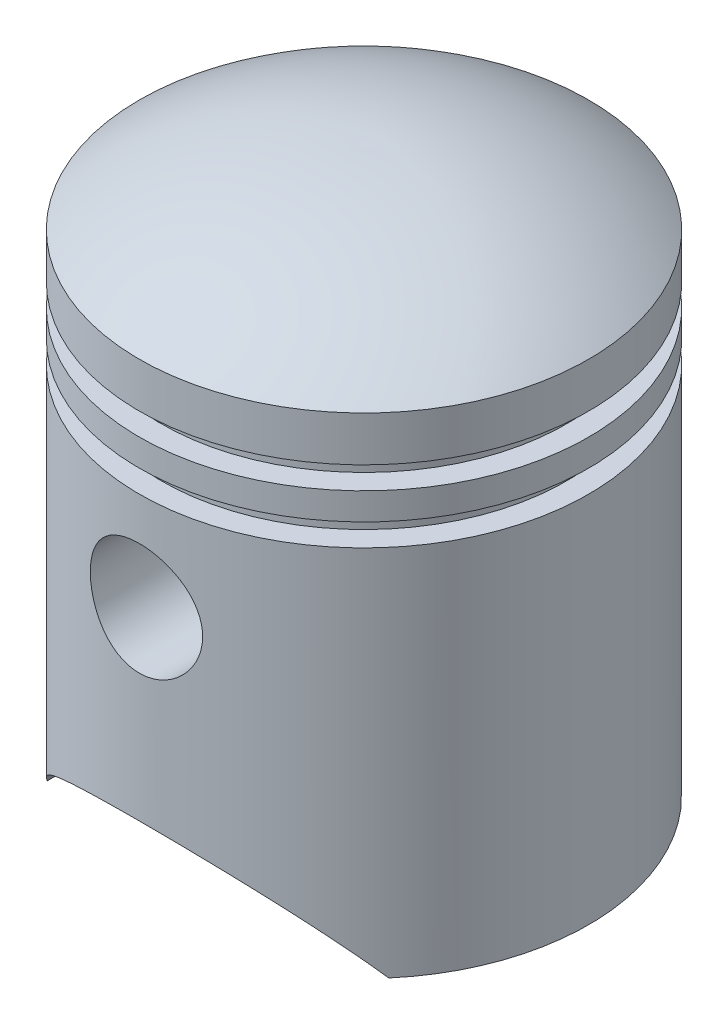
SolidWorks part; units mm, degrees
ref_plane "Front Plane" through (0, 0, 0) normal (0, 0, 1) x (1, 0, 0)
ref_plane "Top Plane" through (0, 0, 0) normal (0, 1, 0) x (1, 0, 0)
ref_plane "Right Plane" through (0, 0, 0) normal (1, 0, 0) x (0, 0, -1)
sketch "Sketch1" plane through (0, 0, 0) normal (0, 0, 1) x (1, 0, 0)
  line L0 (0, 1587.5) -> (0, 1536.6838)
  line L1 (584.2, 0) -> (635, 0)
  line L2 (635, 0) -> (635, 1054.1)
  line L3 (635, 1054.1) -> (571.5, 1054.1)
  line L4 (571.5, 1054.1) -> (571.5, 1117.6)
  line L5 (571.5, 1117.6) -> (635, 1117.6)
  line L6 (635, 1117.6) -> (635, 1193.8)
  line L7 (635, 1193.8) -> (571.5, 1193.8)
  line L8 (571.5, 1193.8) -> (571.5, 1257.3)
  line L9 (571.5, 1257.3) -> (635, 1257.3)
  line L10 (635, 1257.3) -> (635, 1384.3)
  line L13 (584.2, 0) -> (584.2, 1003.3)
  line L14 (584.2, 1003.3) -> (520.7, 1003.3)
  line L15 (520.7, 1003.3) -> (520.7, 1155.7)
  line L16 (520.7, 1155.7) -> (520.7, 1155.7)
  line L17 (520.7, 1155.7) -> (520.7, 1155.7)
  line L18 (520.7, 1155.7) -> (520.7, 1155.7)
  line L19 (520.7, 1155.7) -> (520.7, 1308.1)
  line L20 (520.7, 1308.1) -> (584.2, 1308.1)
  line L21 (584.2, 1308.1) -> (584.2, 1358.5066)
  line L22 (584.2, 50.8) -> (584.2, 1003.3) construction
  line L23 (50.8, 50.8) -> (584.2, 50.8) construction
  line L24 (0, 0) -> (635, 0) construction
  line L25 (0, 1587.5) -> (0, 0) construction
  line L26 (50.8, 1536.6622) -> (50.8, 50.8) construction
  arc A0 (635, 1384.3) -> (0, 1587.5) centre (24.9904, 571.8074) ccw
  arc A1 (584.2, 1358.5066) -> (0, 1536.6838) centre (24.9904, 571.8074) ccw
  arc A2 (584.2, 1358.5066) -> (50.8, 1536.6622) centre (24.9904, 571.8074) ccw construction
  dimension "D8" = 1016
  dimension "D3" = 1054.1
  dimension "D4" = 63.5
  dimension "D5" = 63.5
  dimension "D6" = 76.2
  dimension "D7" = 127
  dimension "D9" = 50.8
revolve "Revolve2" add sketch "Sketch1" angle 360 about L0
sketch "Sketch2" plane through (0, 0, 0) normal (0, 0, 1) x (1, 0, 0)
  line L0 (-482.6, 0) -> (482.6, 0)
  line L1 (-635, 0) -> (635, 0) construction
  line L2 (0, 0) -> (0, 254) construction
  arc A0 (482.6, 0) -> (-482.6, 0) centre (0, -331.196) ccw
  dimension "D1" = 254
  dimension "D2" = 965.2
extrude "Cut-Extrude1" cut sketch "Sketch2" against normal mid plane 1369.568
sketch "Sketch3" plane through (0, 0, 0) normal (0, 0, 1) x (1, 0, 0)
  line L0 (0, 774.7) -> (0, 1587.5) construction
  circle A0 centre (0, 774.7) radius 158.75
  point P2 (0, 0)
  dimension "D2" = 317.5
  dimension "D1" = 812.8
extrude "Cut-Extrude2" cut sketch "Sketch3" against normal mid plane 1912.62
ref_plane "Plane1" through (0, 0, 304.8) normal (0, 0, 1) x (1, 0, 0)
sketch "Sketch5" plane through (0, 0, 304.8) normal (0, 0, 1) x (1, 0, 0)
  circle A0 centre (0, 774.7) radius 158.75 construction
  circle A1 centre (0, 774.7) radius 158.75
  circle A2 centre (0, 774.7) radius 184.15
  dimension "D1" = 368.3
extrude "Boss-Extrude1" add sketch "Sketch5" along normal up to next
mirror "Mirror1" about plane through (0, 0, 0) normal (0, 0, 1) of "Boss-Extrude1"
